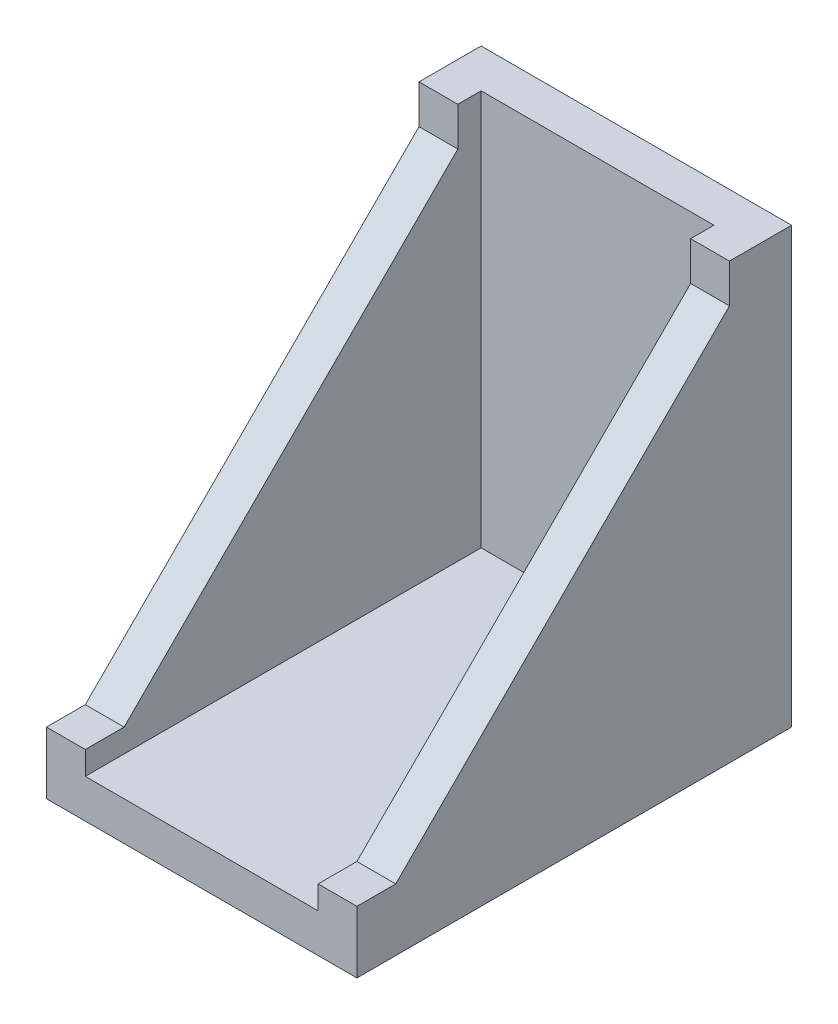
SolidWorks part; units mm, degrees
ref_plane "Front Plane" through (0, 0, 0) normal (0, 0, 1) x (1, 0, 0)
ref_plane "Top Plane" through (0, 0, 0) normal (0, 1, 0) x (1, 0, 0)
ref_plane "Right Plane" through (0, 0, 0) normal (1, 0, 0) x (0, 0, -1)
sketch "Sketch1" plane through (0, 0, 0) normal (0, 1, 0) x (1, 0, 0)
  line L1 (0, 0) -> (20, 0)
  line L2 (0, 0) -> (0, -28)
  line L3 (0, -28) -> (20, -28)
  line L4 (20, 0) -> (20, -28)
  dimension "D1" = 28
  dimension "D2" = 20
extrude "Boss-Extrude1" add sketch "Sketch1" along normal blind 28
sketch "Sketch2" plane through (0, 28, 0) normal (0, 1, 0) x (1, 0, 0)
  line L0 (0, -28) -> (20, -28) construction
  line L1 (2.5, -28) -> (17.5, -28)
  line L2 (2.5, -28) -> (2.5, -2.5)
  line L3 (2.5, -2.5) -> (17.5, -2.5)
  line L4 (17.5, -28) -> (17.5, -2.5)
  line L5 (10, -28) -> (10, 0) construction
  line L6 (20, 0) -> (0, 0) construction
  line L7 (20, -28) -> (20, 0) construction
  point P10 (10, -28)
  dimension "D1" = 2.5
  dimension "D2" = 2.5
extrude "Cut-Extrude1" cut sketch "Sketch2" against normal blind 25.5
ref_plane "Plane1" through (10, 0, 0) normal (-1, 0, 0) x (0, 0, 1)
sketch "Sketch3" plane through (10, 0, 0) normal (-1, 0, 0) x (0, 0, 1)
  line L0 (4, 28) -> (4, 25.5)
  line L1 (28, 28) -> (0, 28) construction
  line L2 (4, 25.5) -> (25.5, 4)
  line L3 (25.5, 4) -> (28, 4)
  line L4 (28, 28) -> (28, 0) construction
  line L5 (28, 28) -> (28, 4)
  line L6 (28, 28) -> (4, 28)
  dimension "D1" = 45
  dimension "D2" = 24
  dimension "D3" = 24
  dimension "D4" = 2.5
extrude "Cut-Extrude2" cut sketch "Sketch3" against normal up to next and the other way up to next
equation "\"D2@Sketch2\"=\"D1@Sketch2\""
